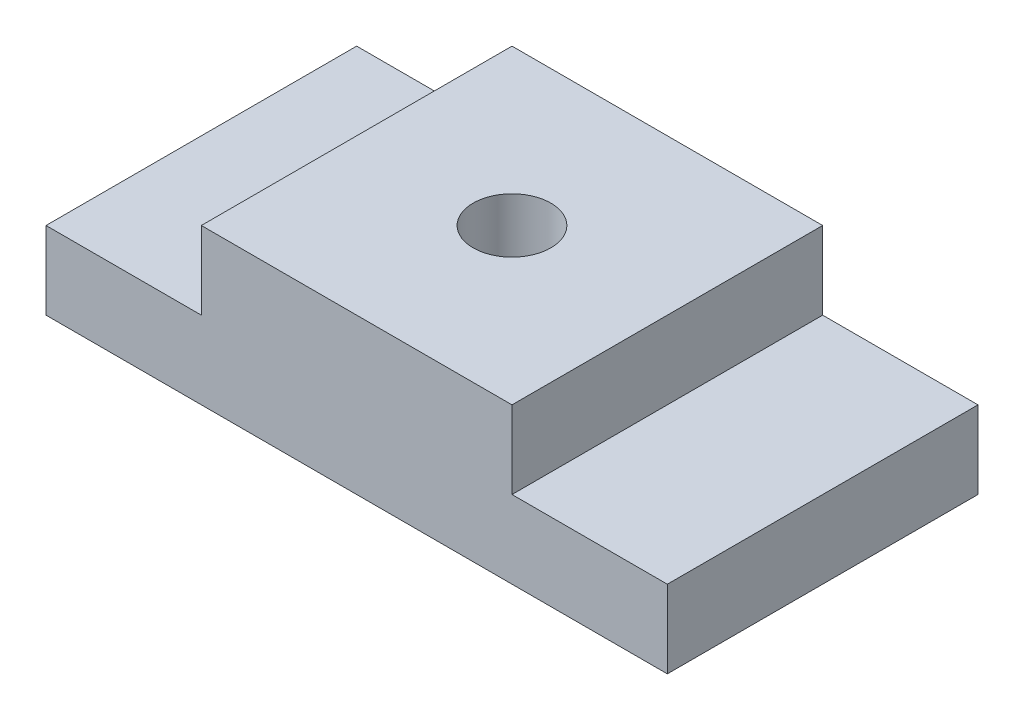
SolidWorks part; units mm, degrees
ref_plane "Front Plane" through (0, 0, 0) normal (0, 0, 1) x (1, 0, 0)
ref_plane "Top Plane" through (0, 0, 0) normal (0, 1, 0) x (1, 0, 0)
ref_plane "Right Plane" through (0, 0, 0) normal (1, 0, 0) x (0, 0, -1)
sketch "Sketch1" plane through (0, 0, 0) normal (0, 1, 0) x (1, 0, 0)
  line L1 (-40, -20) -> (40, -20)
  line L2 (-40, -20) -> (-40, 20)
  line L3 (-40, 20) -> (40, 20)
  line L4 (40, -20) -> (40, 20)
  line L5 (-40, -20) -> (40, 20) construction
  line L6 (-40, 20) -> (40, -20) construction
  point P0 (0, 0)
  dimension "D1" = 40
  dimension "D2" = 80
extrude "Boss-Extrude1" add sketch "Sketch1" along normal blind 10
sketch "Sketch2" plane through (0, 10, 0) normal (0, 1, 0) x (1, 0, 0)
  line L0 (40, 20) -> (-40, 20) construction
  line L1 (-20, -20) -> (20, -20)
  line L2 (-20, -20) -> (-20, 20)
  line L3 (-20, 20) -> (20, 20)
  line L4 (20, -20) -> (20, 20)
  line L5 (-20, -20) -> (20, 20) construction
  line L6 (-20, 20) -> (20, -20) construction
  point P0 (0, 0)
  dimension "D1" = 40
extrude "Boss-Extrude2" add sketch "Sketch2" along normal blind 10
sketch "Sketch3" plane through (0, 20, 0) normal (0, 1, 0) x (1, 0, 0)
  circle A0 centre (0, 0) radius 5
  dimension "D1" = 10
extrude "Cut-Extrude1" cut sketch "Sketch3" against normal blind 10
sketch "Sketch4" plane through (0, 10, 0) normal (0, 1, 0) x (1, 0, 0)
  circle A0 centre (0, 0) radius 5
extrude "Boss-Extrude3" add sketch "Sketch4" along normal blind 10
sketch "Sketch5" plane through (0, 20, 0) normal (0, 1, 0) x (1, 0, 0)
  circle A0 centre (0, 0) radius 5
extrude "Cut-Extrude2" cut sketch "Sketch5" against normal blind 10 contours A0
